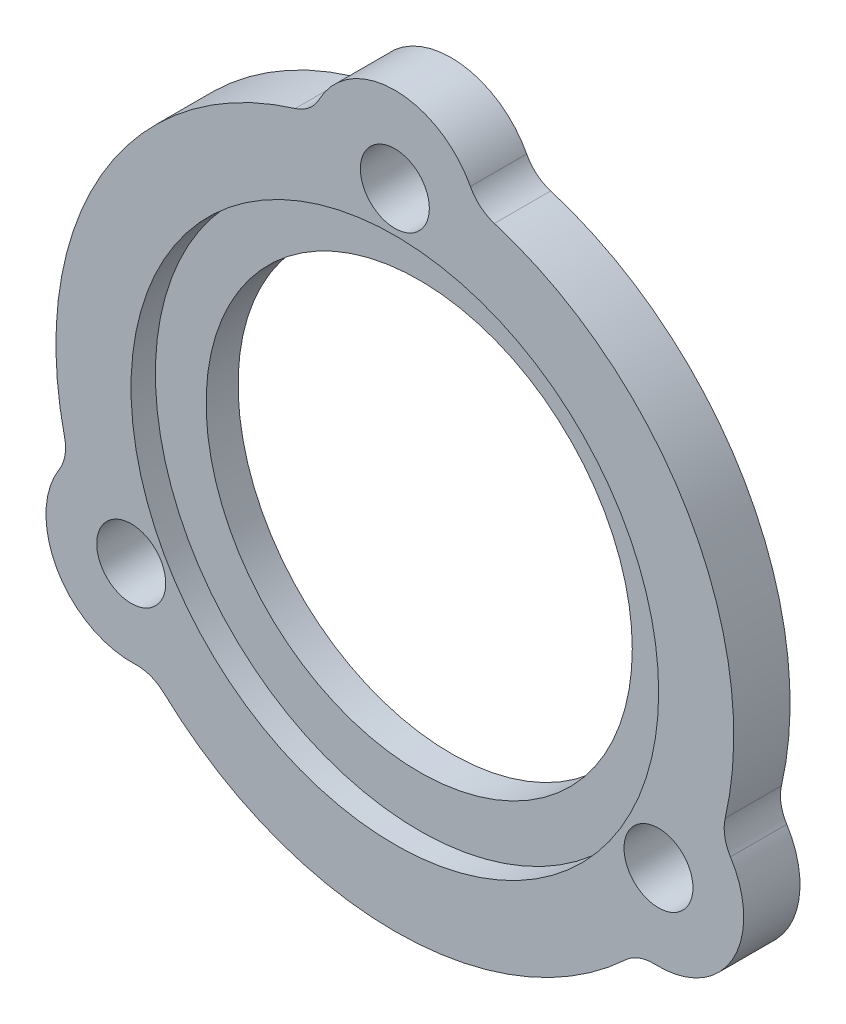
SolidWorks part; units mm, degrees
material "PA Type 6"
ref_plane "Front Plane" through (0, 0, 0) normal (0, 0, 1) x (1, 0, 0)
ref_plane "Top Plane" through (0, 0, 0) normal (0, 1, 0) x (1, 0, 0)
ref_plane "Right Plane" through (0, 0, 0) normal (1, 0, 0) x (0, 0, -1)
sketch "Sketch1" plane through (0, 0, 0) normal (0, 0, 1) x (1, 0, 0)
  line L0 (0, 19.05) -> (0, 0) construction
  circle A0 centre (0, 19.05) radius 2.159
  circle A1 centre (16.4978, -9.525) radius 2.159
  circle A2 centre (-16.4978, -9.525) radius 2.159
  circle A3 centre (0, 0) radius 19.05 construction
  circle A4 centre (0, 0) radius 16.51
  arc A5 (-4.3282, 15.9326) -> (0, 13.716) centre (0, 19.05) ccw
  arc A6 (15.2725, -14.7164) -> (20.381, -5.8682) centre (16.4978, -9.525) ccw
  arc A7 (-20.381, -5.8682) -> (-15.2725, -14.7164) centre (-16.4978, -9.525) ccw
  arc A8 (-5.1085, 20.5846) -> (-20.381, -5.8682) centre (0, 0) ccw
  circle A9 centre (0, 19.05) radius 5.334 construction
  arc A10 (5.1085, 20.5846) -> (-5.1085, 20.5846) centre (0, 19.05) ccw
  circle A11 centre (16.4978, -9.525) radius 5.334 construction
  circle A12 centre (-16.4978, -9.525) radius 5.334 construction
  arc A13 (-15.2725, -14.7164) -> (15.2725, -14.7164) centre (0, 0) ccw
  arc A14 (20.381, -5.8682) -> (5.1085, 20.5846) centre (0, 0) ccw
  point P11 (0, 0)
  dimension "D1" = 4.318
  dimension "D4" = 38.1
  dimension "D5" = 33.02
  dimension "D2" = 19.05
  dimension "D6" = 3.175
  dimension "D3" = 3
extrude "Boss-Extrude1" add sketch "Sketch1" along normal blind 1.524 contours A6 A14 A10 A8 A7 A13 A0 A1 A2 A4
sketch "Sketch2" plane through (0, 0, 0) normal (0, 0, 1) x (1, 0, 0)
  circle A0 centre (0, 0) radius 13.335
  circle A1 centre (0, 0) radius 16.51 construction
  circle A2 centre (16.4978, -9.525) radius 2.159 construction
  circle A3 centre (-16.4978, -9.525) radius 2.159 construction
  circle A4 centre (0, 19.05) radius 2.159 construction
  circle A5 centre (16.4978, -9.525) radius 2.159
  arc A6 (15.2725, -14.7164) -> (20.381, -5.8682) centre (16.4978, -9.525) ccw
  arc A7 (20.381, -5.8682) -> (5.1085, 20.5846) centre (0, 0) ccw
  arc A8 (5.1085, 20.5846) -> (-5.1085, 20.5846) centre (0, 19.05) ccw
  arc A9 (-5.1085, 20.5846) -> (-20.381, -5.8682) centre (0, 0) ccw
  arc A10 (-20.381, -5.8682) -> (-15.2725, -14.7164) centre (-16.4978, -9.525) ccw
  arc A11 (-15.2725, -14.7164) -> (15.2725, -14.7164) centre (0, 0) ccw
  arc A12 (15.2725, -14.7164) -> (20.381, -5.8682) centre (16.4978, -9.525) ccw
  arc A13 (20.381, -5.8682) -> (5.1085, 20.5846) centre (0, 0) ccw
  arc A14 (5.1085, 20.5846) -> (-5.1085, 20.5846) centre (0, 19.05) ccw
  arc A15 (-5.1085, 20.5846) -> (-20.381, -5.8682) centre (0, 0) ccw
  arc A16 (-20.381, -5.8682) -> (-15.2725, -14.7164) centre (-16.4978, -9.525) ccw
  arc A17 (-15.2725, -14.7164) -> (15.2725, -14.7164) centre (0, 0) ccw
  circle A18 centre (-16.4978, -9.525) radius 2.159
  circle A19 centre (0, 19.05) radius 2.159
  dimension "D2" = 3.175
  dimension "D1" = 0
extrude "Boss-Extrude2" add sketch "Sketch2" against normal blind 2 contours A16 A17 A12 A13 A14 A15 A19 A18 A0 A5
fillet "Fillet1" radius 2.54 6 edges at (5.1085, 20.5846, -0.238) (20.381, -5.8682, -0.238) (15.2725, -14.7164, -0.238) (-20.381, -5.8682, -0.238) (-15.2725, -14.7164, -0.238) (-5.1085, 20.5846, -0.238)
